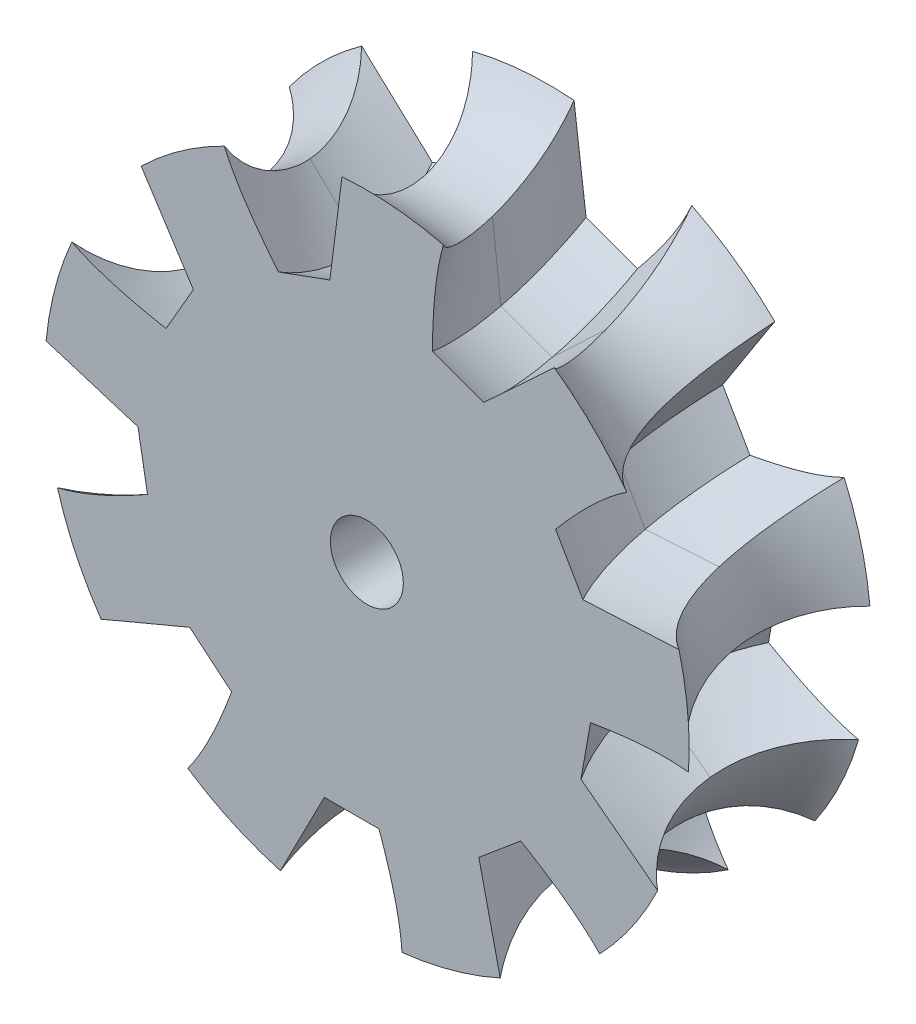
SolidWorks part; units mm, degrees
ref_plane "Front Plane" through (0, 0, 0) normal (0, 0, 1) x (1, 0, 0)
ref_plane "Top Plane" through (0, 0, 0) normal (0, 1, 0) x (1, 0, 0)
ref_plane "Right Plane" through (0, 0, 0) normal (1, 0, 0) x (0, 0, -1)
sketch "Sketch1" plane through (0, 0, 0) normal (0, 0, 1) x (1, 0, 0)
  circle A0 centre (0, 0) radius 21
  circle A1 centre (0, 0) radius 2
  dimension "D1" = 42
  dimension "D2" = 4
extrude "Boss-Extrude1" add sketch "Sketch1" along normal blind 10
chamfer "Chamfer1" distance 2 angle 45 2 edges at (21, 0, 0) (21, 0, 10)
sketch "Sketch2" plane through (0, 0, 0) normal (1, 0, 0) x (0, 0, -1)
  line L0 (0, 0) -> (12.769, 0) construction
  line L1 (0, 0) -> (-5, 0) construction
  line L2 (-5, 0) -> (-5, -21) construction
  circle A0 centre (-5, -21) radius 6
  dimension "D1" = 12
  dimension "D2" = 21
revolve "Cut-Revolve1" cut sketch "Sketch2" angle 360 about L0
sketch "Sketch3" plane through (0, 0, 0) normal (1, 0, 0) x (0, 0, -1)
  circle A1 centre (-5, -21) radius 6
  circle A2 centre (-5, -21) radius 6
  dimension "D1" = 0
curve "Helix/Spiral1" pitch 10 height 2.5 turns 0.25
ref_plane "Plane1" through (0, 0, 5) normal (0, 0, 1) x (1, 0, 0)
sketch "Sketch5" plane through (0, 0, 5) normal (0, 0, 1) x (1, 0, 0)
  line L0 (0, 0) -> (0, -11) construction
  line L1 (-1.5, -11) -> (1.5, -11)
  line L4 (3.5, -15) -> (1.5, -11)
  line L6 (-3.5, -16.5198) -> (3.5, -16.5198)
  line L7 (3.5, -16.5198) -> (3.5, -15)
  line L8 (-3.5, -16.5198) -> (-3.5, -15)
  line L9 (-3.5, -15) -> (-1.5, -11)
  point P9 (0, -16.5198)
  dimension "D1" = 11
  dimension "D2" = 3
  dimension "D3" = 4
  dimension "D4" = 7
sweep "Cut-Sweep1" cut profiles "Sketch5" path "Helix/Spiral1"
sketch "Sketch6" plane through (0, 0, 0) normal (1, 0, 0) x (0, 0, -1)
  circle A1 centre (-5, -21) radius 6
  circle A2 centre (-5, -21) radius 6
  dimension "D1" = 0
curve "Helix/Spiral2" pitch 10 height 2.5 turns 0.25
sketch "Sketch7" plane through (0, 0, 5) normal (0, 0, 1) x (1, 0, 0)
  line L6 (1.5, -11) -> (-1.5, -11)
  line L7 (3.5, -15) -> (1.5, -11)
  line L8 (3.5, -16.5198) -> (3.5, -15)
  line L9 (-3.5, -16.5198) -> (3.5, -16.5198)
  line L10 (-3.5, -15) -> (-3.5, -16.5198)
  line L11 (-1.5, -11) -> (-3.5, -15)
  line L12 (1.5, -11) -> (-1.5, -11)
  line L13 (3.5, -15) -> (1.5, -11)
  line L14 (3.5, -16.5198) -> (3.5, -15)
  line L15 (-3.5, -16.5198) -> (3.5, -16.5198)
  line L16 (-3.5, -15) -> (-3.5, -16.5198)
  line L17 (-1.5, -11) -> (-3.5, -15)
  dimension "D1" = 0
sweep "Cut-Sweep2" cut profiles "Sketch7" path "Helix/Spiral2"
pattern_circular "CirPattern1" count 9 over 360 about axis through (0, 0, 10) along (0, 0, -1) of "Cut-Sweep1", "Cut-Sweep2"
